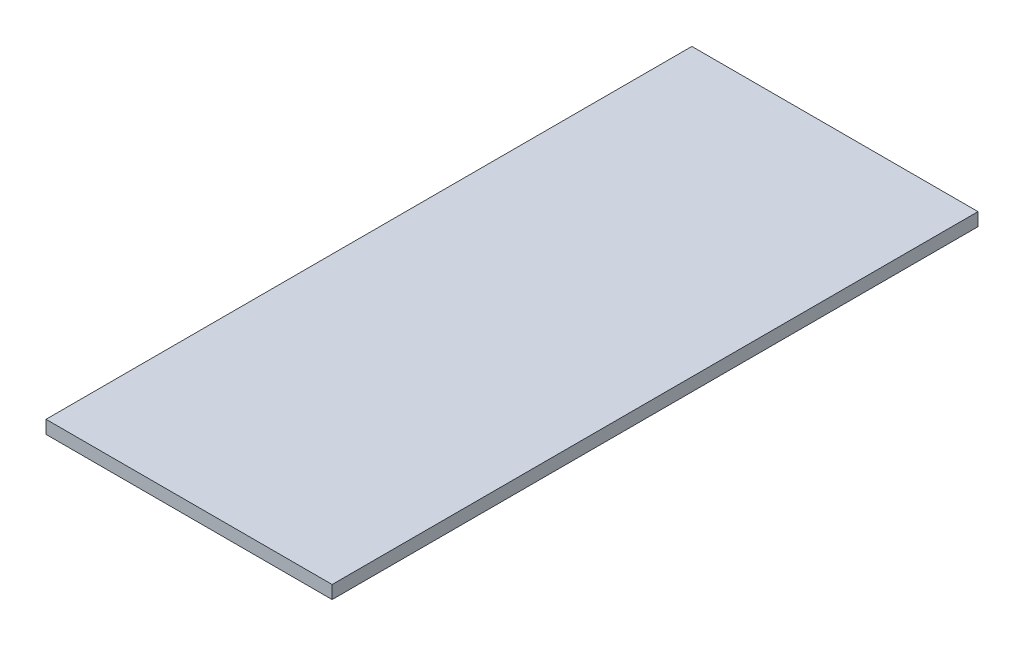
SolidWorks part; units mm, degrees
ref_plane "前视基准面" through (0, 0, 0) normal (0, 0, 1) x (1, 0, 0)
ref_plane "上视基准面" through (0, 0, 0) normal (0, 1, 0) x (1, 0, 0)
ref_plane "右视基准面" through (0, 0, 0) normal (1, 0, 0) x (0, 0, -1)
sketch "草图1" plane through (0, 4.0295, 0) normal (0, 1, 0) x (1, 0, 0)
  line L1 (2.25, -70.8633) -> (-15.25, -70.8633)
  line L2 (2.25, -70.8633) -> (2.25, -31.3633)
  line L3 (2.25, -31.3633) -> (-15.25, -31.3633)
  line L4 (-15.25, -70.8633) -> (-15.25, -31.3633)
extrude "凸台-拉伸1" add sketch "草图1" along normal blind 0.8
